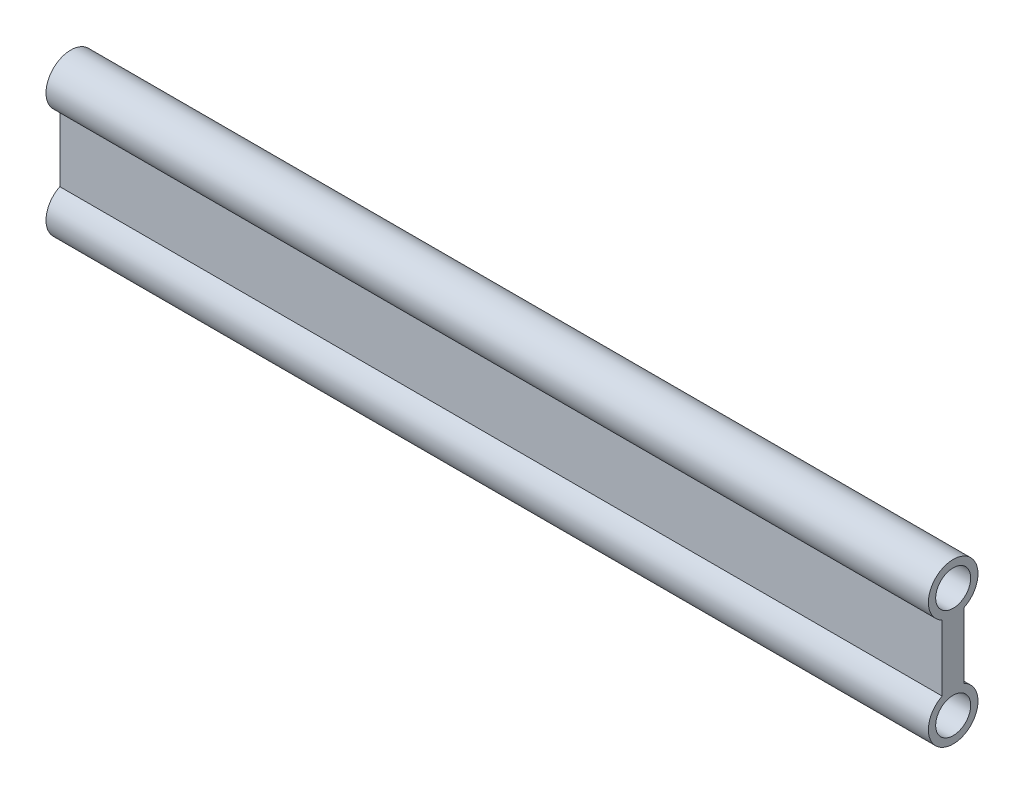
SolidWorks part; units mm, degrees
ref_plane "Front Plane" through (0, 0, 0) normal (0, 0, 1) x (1, 0, 0)
ref_plane "Top Plane" through (0, 0, 0) normal (0, 1, 0) x (1, 0, 0)
ref_plane "Right Plane" through (0, 0, 0) normal (1, 0, 0) x (0, 0, -1)
sketch "Sketch1" plane through (0, 0, 0) normal (1, 0, 0) x (0, 0, -1)
  line L0 (-2, 15.9689) -> (-2, 4.0311)
  line L1 (2, 15.9689) -> (2, 4.0311)
  circle A0 centre (0, 0) radius 3.175
  circle A1 centre (0, 20) radius 3.175
  arc A2 (-2, 4.0311) -> (2, 4.0311) centre (0, 0) ccw
  arc A3 (2, 15.9689) -> (-2, 15.9689) centre (0, 20) ccw
  point P11 (0, 0)
  dimension "D2" = 6.35
  dimension "D3" = 6.35
  dimension "D4" = 9
  dimension "D5" = 9
  dimension "D1" = 20
  dimension "D6" = 2
  dimension "D7" = 2
extrude "Boss-Extrude1" add sketch "Sketch1" along normal blind 160
